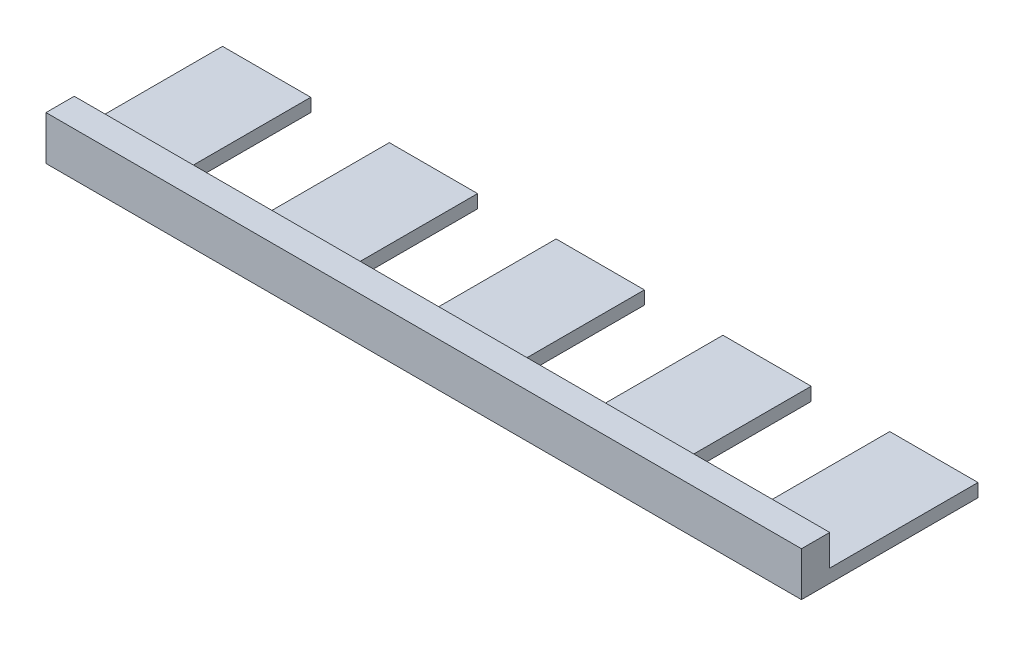
SolidWorks part; units mm, degrees
ref_plane "Ebene vorne" through (0, 0, 0) normal (0, 0, 1) x (1, 0, 0)
ref_plane "Ebene oben" through (0, 0, 0) normal (0, 1, 0) x (1, 0, 0)
ref_plane "Ebene rechts" through (0, 0, 0) normal (1, 0, 0) x (0, 0, -1)
sketch "Skizze1" plane through (0, 0, 0) normal (0, 1, 0) x (1, 0, 0)
  line L0 (0, 0) -> (0, 40)
  line L1 (0, 40) -> (20, 40)
  line L2 (20, 40) -> (20, 6.4)
  line L3 (20, 6.4) -> (37.8, 6.4)
  line L4 (37.8, 6.4) -> (37.8, 40)
  line L5 (37.8, 40) -> (57.8, 40)
  line L6 (57.8, 40) -> (57.8, 6.4)
  line L7 (57.8, 6.4) -> (75.6, 6.4)
  line L8 (75.6, 6.4) -> (75.6, 40)
  line L9 (75.6, 40) -> (95.6, 40)
  line L10 (0, 0) -> (171.2, 0)
  line L11 (0, 40) -> (171.2, 40) construction
  line L12 (20, 6.4) -> (75.6, 6.4) construction
  line L13 (85.6, 40) -> (85.6, 0.1224) construction
  line L14 (151.2, 6.4) -> (95.6, 6.4) construction
  line L15 (95.6, 6.4) -> (95.6, 40)
  line L16 (113.4, 6.4) -> (95.6, 6.4)
  line L17 (113.4, 40) -> (113.4, 6.4)
  line L18 (133.4, 40) -> (113.4, 40)
  line L19 (133.4, 6.4) -> (133.4, 40)
  line L20 (151.2, 6.4) -> (133.4, 6.4)
  line L21 (151.2, 40) -> (151.2, 6.4)
  line L22 (171.2, 40) -> (151.2, 40)
  line L23 (171.2, 0) -> (171.2, 40)
  line L24 (20, 6.4) -> (0, 6.4)
  point P20 (85.6, 0)
  point P21 (85.6, 40)
other "Stiftskizze1" parameters "D1"=37.1126, "D2"=39.75, "D3"=10.5, "D4"=39.75, "D5"=39.75, "D6"=15, "D7"=73.1
extrude "Aufsatz-Linear austragen1" add sketch "Skizze1" along normal blind 3 contours L24 L2 L1 L0 | L3 L24 L0 L10 L23 L22 L21 L20 L19 L18 L17 L16 L15 L9 L8 L7 L6 L5 L4
sketch "Skizze3" plane through (0, 3, 0) normal (0, 1, 0) x (1, 0, 0)
  line L1 (0, 6.4) -> (171.2, 6.4)
  line L2 (0, 6.4) -> (0, 0)
  line L3 (0, 0) -> (171.2, 0)
  line L4 (171.2, 6.4) -> (171.2, 0)
extrude "Aufsatz-Linear austragen2" add sketch "Skizze3" along normal blind 7
